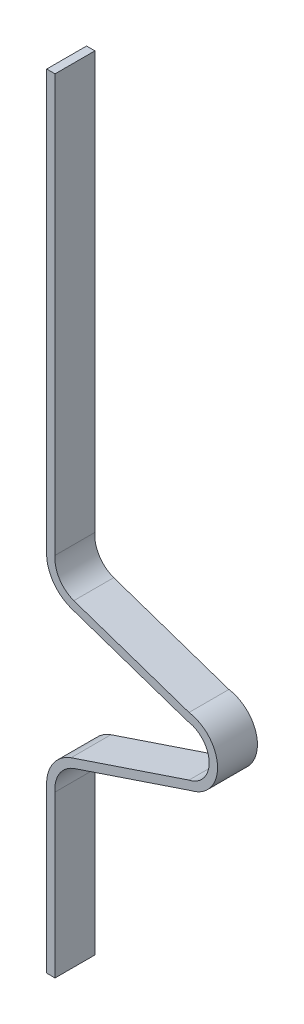
SolidWorks part; units mm, degrees
material "POLIURETANO (11671)"
ref_plane "Front Plane" through (0, 0, 0) normal (0, 0, 1) x (1, 0, 0)
ref_plane "Top Plane" through (0, 0, 0) normal (0, 1, 0) x (1, 0, 0)
ref_plane "Right Plane" through (0, 0, 0) normal (1, 0, 0) x (0, 0, -1)
sketch "Sketch1" plane through (0, 0, 0) normal (0, 0, 1) x (1, 0, 0)
  line L0 (5.9386, 132.6706) -> (23.8531, 126.5755)
  line L1 (23, 121.3613) -> (29.1221, 121.3613) construction
  line L2 (3.0195, 105.4434) -> (3.0195, 19.2747)
  line L3 (5.9377, 110.0814) -> (24.1982, 116.2154)
  line L4 (1.7195, 137.3656) -> (1.7195, 223.4776)
  line L5 (5.5046, 131.445) -> (23.5438, 125.3076)
  line L6 (5.5061, 111.3078) -> (23.8471, 117.4689)
  line L8 (1.7195, 105.3867) -> (1.7195, 19.2747)
  line L9 (3.0195, 137.3089) -> (3.0195, 223.4776)
  line L10 (23, 120.0613) -> (28.2502, 120.0613)
  line L11 (1.7195, 223.4776) -> (3.0195, 223.4776)
  line L12 (1.7195, 19.2747) -> (3.0195, 19.2747)
  line L13 (23, 121.3613) -> (28.2502, 121.3613) construction
  line L14 (23, 121.3613) -> (23.6273, 121.3613) construction
  arc A0 (5.9377, 110.0814) -> (3.0195, 105.4434) centre (7.5, 105.8613) ccw
  arc A1 (24.1982, 116.2154) -> (23.8531, 126.5755) centre (23, 121.3613) ccw
  arc A2 (5.5046, 131.445) -> (1.7195, 137.3656) centre (7.5, 136.891) cw
  arc A3 (23.8471, 117.4689) -> (23.5438, 125.3076) centre (23, 121.3613) ccw
  arc A4 (5.5061, 111.3078) -> (1.7195, 105.3867) centre (7.5, 105.8613) ccw
  arc A5 (5.9377, 110.0814) -> (3.0195, 105.4434) centre (7.5, 105.8613) ccw construction
  arc A6 (5.9386, 132.6706) -> (3.0195, 137.3089) centre (7.5, 136.891) cw
  circle A8 centre (7.5, 105.8613) radius 2.8 construction
  circle A9 centre (23, 121.3613) radius 2.5
  circle A10 centre (7.5, 136.891) radius 2.7915 construction
  point P5 (1.3, -104.3084)
  point P17 (22.8582, 121.3762)
  point P21 (0, -104.3084)
  point P22 (0, 223.4133)
  dimension "D2" = 4.5
  dimension "D3" = 3.9835
  dimension "D1" = 1.3
extrude "Boss-Extrude1" add sketch "Sketch1" against normal blind 6.2 contours L4 L11 L9 A6 L0 A1 L3 A0 L2 L12 L8 A4 L6 A3 L5 A2
sketch "Sketch2" plane through (1.7195, 0, 0) normal (-1, 0, 0) x (0, 0, 1)
  line L1 (4.2929, 12.6804) -> (-18.6501, 12.6804)
  line L2 (4.2929, 12.6804) -> (4.2929, 46.3139)
  line L3 (4.2929, 46.3139) -> (-18.6501, 46.3139)
  line L4 (-18.6501, 12.6804) -> (-18.6501, 46.3139)
extrude "Cut-Extrude1" cut sketch "Sketch2" against normal blind 10
sketch "Sketch3" plane through (3.0195, 0, 0) normal (1, 0, 0) x (0, 0, -1)
  line L0 (6.2, 223.4776) -> (0, 223.4776) construction
  line L1 (6.2, 223.4776) -> (0, 223.4776)
  line L2 (6.2, 223.4776) -> (6.2, 202.142)
  line L3 (6.2, 202.142) -> (0, 202.142)
  line L4 (0, 223.4776) -> (0, 202.142)
  line L5 (6.2, 137.3089) -> (6.2, 223.4776) construction
  line L6 (0, 137.3089) -> (0, 223.4776) construction
extrude "Cut-Extrude2" cut sketch "Sketch3" against normal blind 10
sketch "Sketch4" plane through (3.0195, 0, 0) normal (1, 0, 0) x (0, 0, -1)
  line L0 (0, 105.4434) -> (0, 46.3139) construction
  line L1 (6.2, 46.3139) -> (0, 46.3139)
  line L2 (6.2, 46.3139) -> (6.2, 80.4064)
  line L3 (6.2, 80.4064) -> (0, 80.4064)
  line L4 (0, 46.3139) -> (0, 80.4064)
extrude "Cut-Extrude3" cut sketch "Sketch4" against normal blind 10
